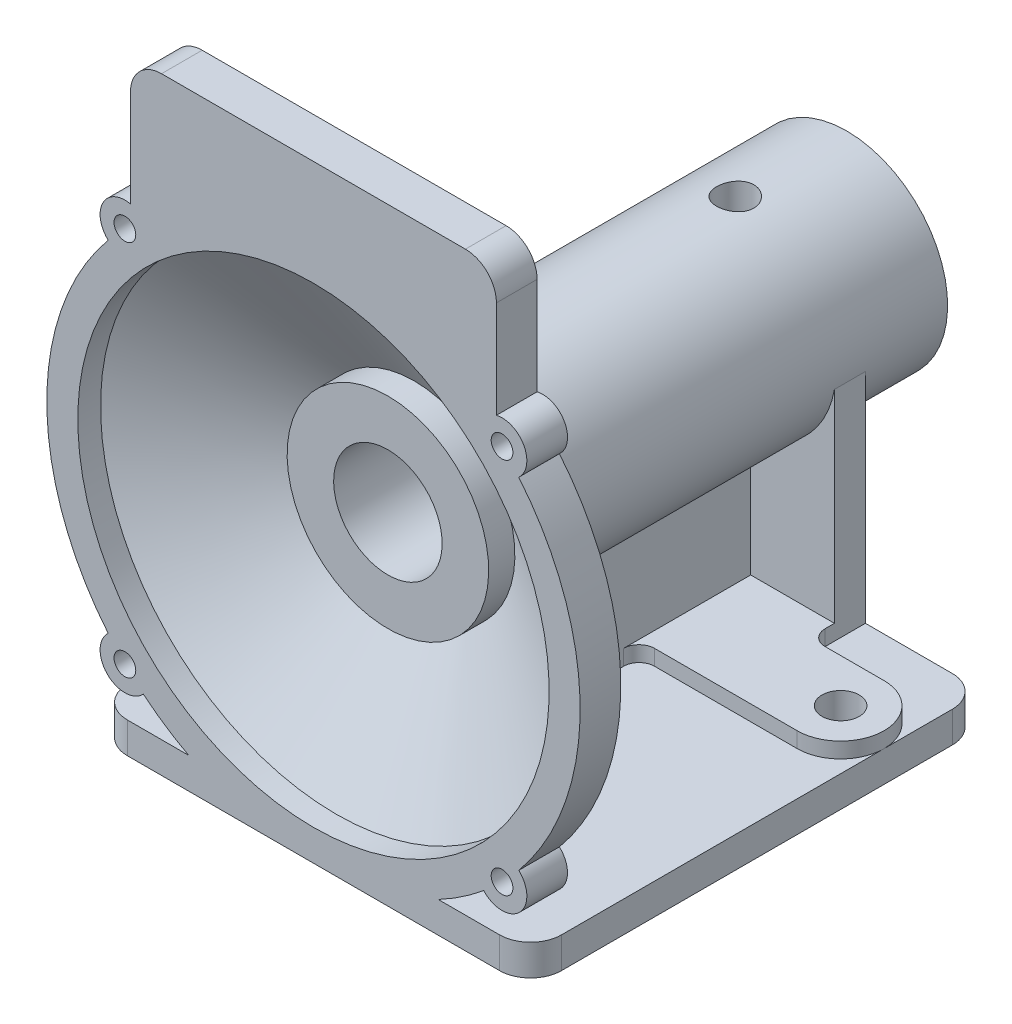
SolidWorks part; units mm, degrees
material "AISI 1020"
ref_plane "Front Plane" through (0, 0, 0) normal (0, 0, 1) x (1, 0, 0)
ref_plane "Top Plane" through (0, 0, 0) normal (0, 1, 0) x (1, 0, 0)
ref_plane "Right Plane" through (0, 0, 0) normal (1, 0, 0) x (0, 0, -1)
sketch "Sketch1" plane through (0, 0, 0) normal (1, 0, 0) x (0, 0, -1)
  line L0 (0, 0) -> (-194.0812, 0) construction
  line L1 (0, 32.5) -> (-128, 32.5)
  line L2 (0, 32.5) -> (0, 17.5)
  line L3 (0, 17.5) -> (-50, 17.5)
  line L4 (-50, 17.5) -> (-50, 21)
  line L5 (-50, 21) -> (-100, 21)
  line L6 (-100, 21) -> (-100, 17.5)
  line L7 (-100, 17.5) -> (-148, 17.5)
  line L8 (-148, 17.5) -> (-148, 32.5)
  line L9 (-148, 32.5) -> (-139.547, 32.5)
  line L10 (-139.547, 32.5) -> (-164.6617, 76)
  line L11 (-164.6617, 76) -> (-172, 76)
  line L12 (-172, 76) -> (-172, 86)
  line L13 (-172, 86) -> (-158.8882, 86)
  line L14 (-158.8882, 86) -> (-128, 32.5)
  dimension "D1" = 65
  dimension "D2" = 35
  dimension "D3" = 50
  dimension "D4" = 42
  dimension "D5" = 50
  dimension "D6" = 48
  dimension "D7" = 172
  dimension "D8" = 152
  dimension "D9" = 172
  dimension "D10" = 10
  dimension "D11" = 128
  dimension "D12" = 120
revolve "Revolve1" add sketch "Sketch1" angle 360 about L0
ref_plane "Plane1" through (0, -86, 0) normal (0, 1, 0) x (1, 0, 0)
sketch "Sketch2" plane through (0, -86, 0) normal (0, 1, 0) x (1, 0, 0)
  line L0 (-86, -172) -> (86, -172) construction
  line L1 (-70, -172) -> (70, -172)
  line L2 (-70, -172) -> (-70, -26)
  line L3 (-70, -26) -> (70, -26)
  line L4 (70, -172) -> (70, -26)
  line L5 (0, 0) -> (0, -202.0602) construction
  dimension "D1" = 140
  dimension "D2" = 146
extrude "Boss-Extrude1" add sketch "Sketch2" along normal blind 10
sketch "Sketch3" plane through (0, 0, 0) normal (1, 0, 0) x (0, 0, -1)
  line L0 (-26, -76) -> (-26, -32.5)
  line L1 (-128, -32.5) -> (0, -32.5) construction
rib "Rib1" sketch "Sketch3" sketch "Sketch3" thickness 10 extrusion direction parallel to sketch draft on no parameters "D1"=10
sketch "Sketch4" plane through (0, 0, 26) normal (0, 0, -1) x (-1, 0, 0)
  line L0 (-32, -76) -> (-32, -5.6789)
  line L1 (-70, -76) -> (-5, -76) construction
  line L2 (32, -76) -> (32, -5.6789)
  line L3 (40.2492, -76) -> (5, -76) construction
  line L4 (0, 0) -> (0, -98.4978) construction
  line L5 (-32, -76) -> (32, -76)
  arc A0 (5, -32.1131) -> (-5, -32.1131) centre (0, 0) ccw construction
  arc A1 (5, -32.1131) -> (32, -5.6789) centre (0, 0) ccw
  arc A2 (-32, -5.6789) -> (-5, -32.1131) centre (0, 0) ccw
  arc A3 (-5, -32.1131) -> (5, -32.1131) centre (0, 0) ccw construction
  arc A4 (-5, -32.1131) -> (5, -32.1131) centre (0, 0) ccw
  dimension "D1" = 64
extrude "Boss-Extrude2" add sketch "Sketch4" against normal blind 10
ref_plane "Plane2" through (0, 110, 0) normal (0, 1, 0) x (1, 0, 0)
sketch "Sketch5" plane through (0, 110, 0) normal (0, 1, 0) x (1, 0, 0)
  line L0 (0, 0) -> (0, -184.9916) construction
  line L1 (-86, -158.8882) -> (86, -158.8882) construction
  line L2 (-59, -158.8882) -> (59, -158.8882)
  line L3 (-59, -158.8882) -> (-59, -172)
  line L4 (-59, -172) -> (59, -172)
  line L5 (59, -158.8882) -> (59, -172)
  line L6 (-86, -172) -> (86, -172) construction
  dimension "D1" = 118
extrude "Boss-Extrude3" add sketch "Sketch5" against normal up to next
sketch "Sketch6" plane through (0, -76, 0) normal (0, 1, 0) x (1, 0, 0)
  line L2 (5, -36) -> (5, -72)
  line L3 (5, -72) -> (56, -72)
  line L6 (32, -36) -> (5, -36)
  line L7 (32, -36) -> (32, -44)
  line L9 (32, -44) -> (56, -44)
  arc A0 (56, -72) -> (56, -44) centre (56, -58) ccw
  dimension "D1" = 14
  dimension "D2" = 51
  dimension "D3" = 8
extrude "Boss-Extrude4" add sketch "Sketch6" along normal blind 5
sketch "Sketch7" plane through (0, -71, 0) normal (0, 1, 0) x (1, 0, 0)
  circle A0 centre (56, -58) radius 6
  dimension "D1" = 12
extrude "Cut-Extrude1" cut sketch "Sketch7" against normal through all
mirror "Mirror1" about plane through (0, 0, 0) normal (1, 0, 0) of "Boss-Extrude4", "Cut-Extrude1"
sketch "Sketch8" plane through (0, 0, 172) normal (0, 0, 1) x (1, 0, 0)
  line L0 (0, 69.4608) -> (0, 0) construction
  line L1 (0, 0) -> (77.3098, 77.3098) construction
  line L2 (0, 0) -> (-77.3098, 77.3098) construction
  arc A0 (-59, 62.57) -> (-40.2492, -76) centre (0, 0) ccw construction
  arc A1 (-59, 62.57) -> (-40.2492, -76) centre (0, 0) ccw
  circle A2 centre (-60.8112, 60.8112) radius 8
  circle A3 centre (60.8112, 60.8112) radius 8
  dimension "D2" = 16
  dimension "D1" = 90
extrude "Boss-Extrude5" add sketch "Sketch8" against normal up to surface (13.1118 mm away) contours A2 | A3 up to face at (0, 92.1425, 158.8882)
sketch "Sketch9" plane through (0, 0, 172) normal (0, 0, 1) x (1, 0, 0)
  circle A0 centre (-60.8112, 60.8112) radius 3.5
  circle A1 centre (60.8112, 60.8112) radius 3.5
  dimension "D1" = 7
extrude "Cut-Extrude2" cut sketch "Sketch9" against normal up to next
mirror "Mirror2" about plane through (0, 0, 0) normal (0, 1, 0) of "Boss-Extrude5", "Cut-Extrude2"
sketch "Sketch10" plane through (5, 0, 0) normal (1, 0, 0) x (0, 0, -1)
  line L0 (-172, -86) -> (-26, -86) construction
  line L1 (-172, -76) -> (-172, -86) construction
  circle A0 centre (-114, -56) radius 15
  dimension "D1" = 30
  dimension "D2" = 30
  dimension "D3" = 58
extrude "Cut-Extrude3" cut sketch "Sketch10" against normal through all
sketch "Sketch11" plane through (0, 0, 0) normal (0, 1, 0) x (1, 0, 0)
  line L0 (32.5, 0) -> (-32.5, 0) construction
  circle A0 centre (0, -36) radius 6
  dimension "D1" = 12
  dimension "D2" = 36
extrude "Cut-Extrude4" cut sketch "Sketch11" along normal up to next
fillet "Fillet3" radius 10 2 edges at (-59, 110, 165.4441) (59, 110, 165.4441)
fillet "Fillet4" radius 5 4 edges at (5, -73.5, 72) (-5, -73.5, 72) (-32, -73.5, 44) (32, -73.5, 44)
fillet "Fillet5" radius 10 4 edges at (-70, -81, 26) (-70, -81, 172) (70, -81, 26) (70, -81, 172)
